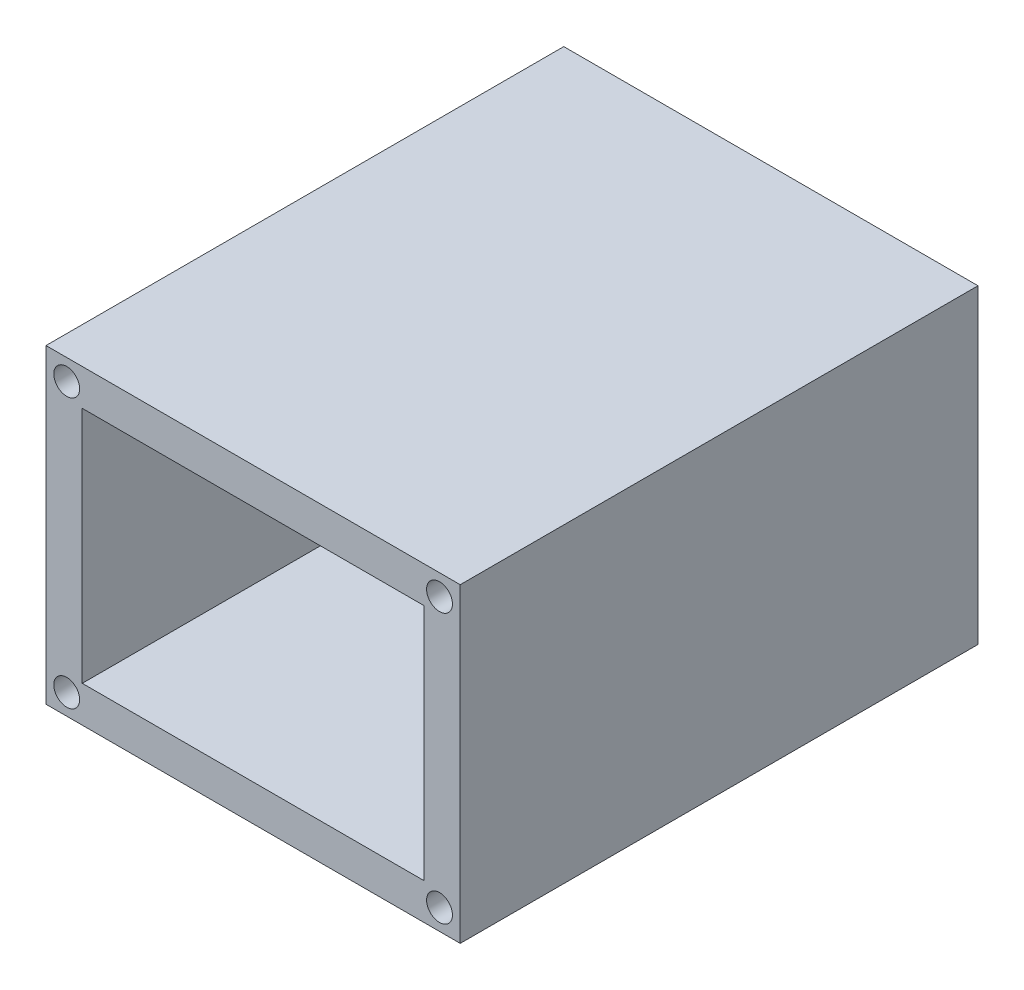
SolidWorks part; units mm, degrees
ref_plane "Front Plane" through (0, 0, 0) normal (0, 0, 1) x (1, 0, 0)
ref_plane "Top Plane" through (0, 0, 0) normal (0, 1, 0) x (1, 0, 0)
ref_plane "Right Plane" through (0, 0, 0) normal (1, 0, 0) x (0, 0, -1)
sketch "Sketch1" plane through (0, 0, 0) normal (0, 0, 1) x (1, 0, 0)
  line L1 (0, 0) -> (40, 0)
  line L2 (0, 0) -> (0, 30)
  line L3 (0, 30) -> (40, 30)
  line L4 (40, 0) -> (40, 30)
  dimension "D1" = 30
  dimension "D2" = 40
extrude "Boss-Extrude1" add sketch "Sketch1" along normal blind 50
sketch "Sketch3" plane through (0, 0, 50) normal (0, 0, 1) x (1, 0, 0)
  line L0 (40, 30) -> (0, 30) construction
  line L1 (3.5, 26.5) -> (36.5, 26.5)
  line L2 (3.5, 26.5) -> (3.5, 3.5)
  line L3 (3.5, 3.5) -> (36.5, 3.5)
  line L4 (36.5, 26.5) -> (36.5, 3.5)
  line L5 (40, 0) -> (40, 30) construction
  point P4 (20, 26.5)
  point P7 (20, 30)
  point P8 (36.5, 15)
  point P11 (40, 15)
  dimension "D1" = 23
  dimension "D2" = 33
extrude "Cut-Extrude1" cut sketch "Sketch3" against normal through all
sketch "Sketch4" plane through (0, 0, 50) normal (0, 0, 1) x (1, 0, 0)
  line L0 (20, 30) -> (20, 27.2489) construction
  line L1 (40, 30) -> (0, 30) construction
  line L2 (38.5104, 15) -> (33.9187, 15) construction
  circle A0 centre (38, 28) radius 1.25
  circle A1 centre (2, 28) radius 1.25
  circle A2 centre (2, 2) radius 1.25
  circle A3 centre (38, 2) radius 1.25
  point P8 (36.2146, 15)
  dimension "D1" = 2.5
  dimension "D2" = 15
  dimension "D3" = 26
  dimension "D4" = 36
extrude "Cut-Extrude2" cut sketch "Sketch4" against normal blind 10
